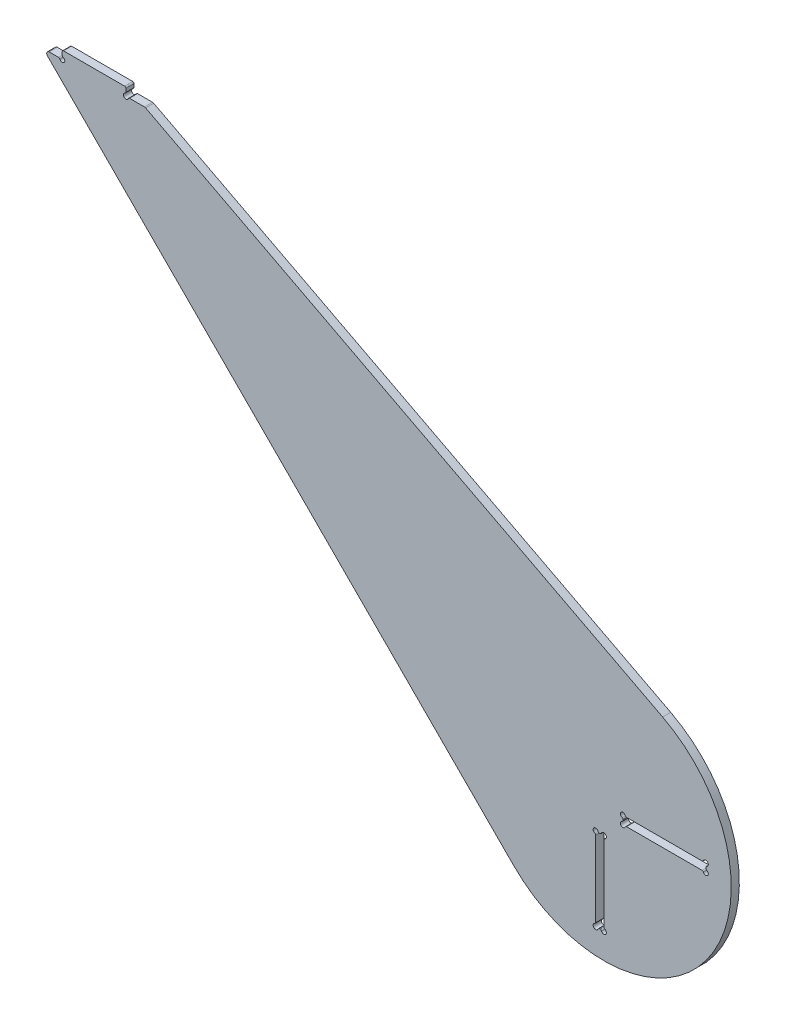
SolidWorks part; units mm, degrees
material "Pine"
ref_plane "Front Plane" through (0, 0, 0) normal (0, 0, 1) x (1, 0, 0)
ref_plane "Top Plane" through (0, 0, 0) normal (0, 1, 0) x (1, 0, 0)
ref_plane "Right Plane" through (0, 0, 0) normal (1, 0, 0) x (0, 0, -1)
sketch "Sketch1" plane through (0, 0, 0) normal (0, 0, 1) x (1, 0, 0)
  line L4 (-360, 300) -> (-440, 300)
  line L5 (-440, 300) -> (-70.8464, -70.5747)
  line L6 (-360, 300) -> (46.1504, 88.7138)
  line L7 (-6.35, -15) -> (0, -15)
  line L8 (-6.35, -15) -> (-6.35, -80)
  line L9 (0, -15) -> (0, -80)
  line L10 (-6.35, -80) -> (0, -80)
  line L11 (15, 0) -> (15, 6.35)
  line L12 (15, 0) -> (80, 0)
  line L13 (15, 6.35) -> (80, 6.35)
  line L14 (80, 0) -> (80, 6.35)
  line L15 (15, 0) -> (0, 0) construction
  line L16 (0, -15) -> (0, 0) construction
  arc A0 (-70.8464, -70.5747) -> (46.1504, 88.7138) centre (0, 0) ccw
  dimension "D1" = 100
  dimension "D2" = 6.35
  dimension "D3" = 80
  dimension "D4" = 65
  dimension "D5" = 15
  dimension "D6" = 15
  dimension "D7" = 440
  dimension "D8" = 300
extrude "Boss-Extrude1" add sketch "Sketch1" along normal mid plane 6.35
sketch "Sketch2" plane through (0, 0, 3.175) normal (0, 0, 1) x (1, 0, 0)
  line L0 (-425, 300) -> (-375, 300)
  line L1 (-425, 300) -> (-425, 306.35)
  line L2 (-375, 300) -> (-375, 306.35)
  line L3 (-425, 306.35) -> (-375, 306.35)
  line L4 (-360, 300) -> (-440, 300) construction
  line L9 (-425, 300) -> (-440, 300) construction
  line L10 (-440, 300) -> (-425, 300) construction
  line L11 (-360, 300) -> (-375, 300) construction
  dimension "D2" = 50
  dimension "D3" = 6.35
extrude "Boss-Extrude2" add sketch "Sketch2" against normal up to surface (6.35 mm away) up to face at (-3.175, -47.5, -3.175)
sketch "Sketch3" plane through (0, 0, 3.175) normal (0, 0, 1) x (1, 0, 0)
  circle A0 centre (-6.35, -15) radius 2
  circle A1 centre (0, -15) radius 2
  circle A2 centre (-6.35, -80) radius 2
  circle A3 centre (0, -80) radius 2
  circle A4 centre (15, 0) radius 2
  circle A5 centre (15, 6.35) radius 2
  circle A6 centre (80, 6.35) radius 2
  circle A7 centre (80, 0) radius 2
  dimension "D1" = 4
extrude "Cut-Extrude1" cut sketch "Sketch3" against normal through all
fillet "Fillet1" radius 1 16 edges at (78, 6.35, 0) (80, 4.35, 0) (80, 2, 0) (78, 0, 0) (17, 0, 0) (17, 6.35, 0) (15, 4.35, 0) (15, 2, 0) (-6.35, -17, 0) (-4.35, -15, 0) (-2, -15, 0) (0, -17, 0) (0, -78, 0) (-2, -80, 0) (-4.35, -80, 0) (-6.35, -78, 0)
sketch "Sketch4" plane through (0, 0, 3.175) normal (0, 0, 1) x (1, 0, 0)
  circle A0 centre (-425, 300) radius 2
  circle A1 centre (-375, 300) radius 2
  dimension "D1" = 4
extrude "Cut-Extrude2" cut sketch "Sketch4" against normal through all
fillet "Fillet2" radius 1 6 edges at (-373, 300, 0) (-375, 302, 0) (-425, 302, 0) (-427, 300, 0) (-425, 306.35, 0) (-375, 306.35, 0)
fillet "Fillet3" radius 2 2 edges at (-360, 300, 0) (-440, 300, 0)
